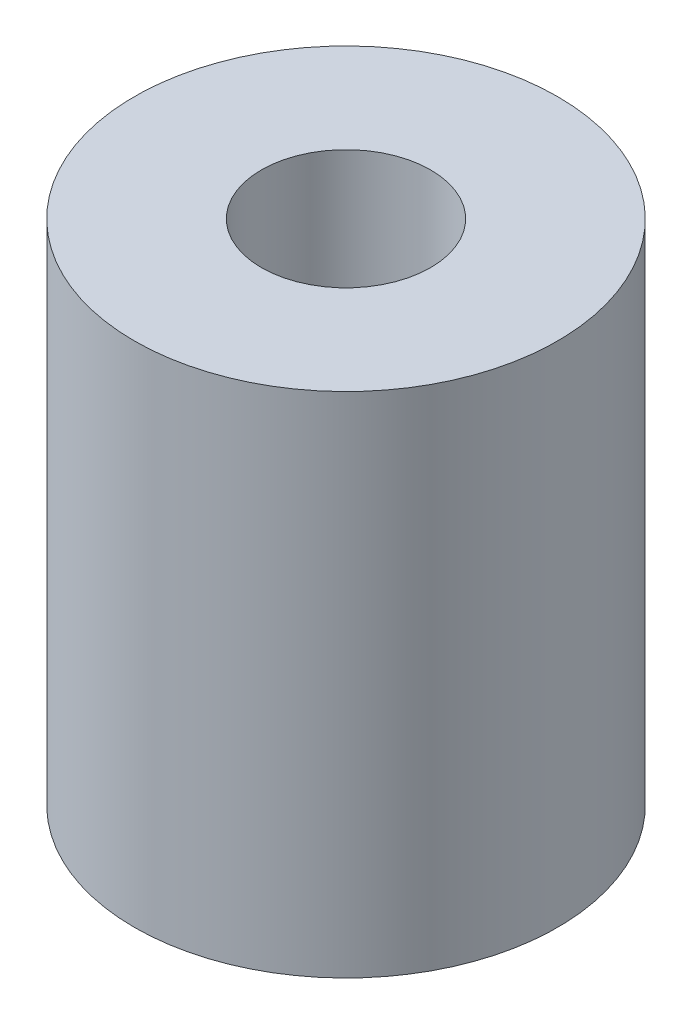
SolidWorks part; units mm, degrees
ref_plane "Front Plane" through (0, 0, 0) normal (0, 0, 1) x (1, 0, 0)
ref_plane "Top Plane" through (0, 0, 0) normal (0, 1, 0) x (1, 0, 0)
ref_plane "Right Plane" through (0, 0, 0) normal (1, 0, 0) x (0, 0, -1)
sketch "Sketch1" plane through (0, 0, 0) normal (0, 1, 0) x (1, 0, 0)
  circle A0 centre (0, 0) radius 2.5
  circle A1 centre (0, 0) radius 1
  dimension "D1" = 2
  dimension "D2" = 5
extrude "Boss-Extrude1" add sketch "Sketch1" along normal blind 6
